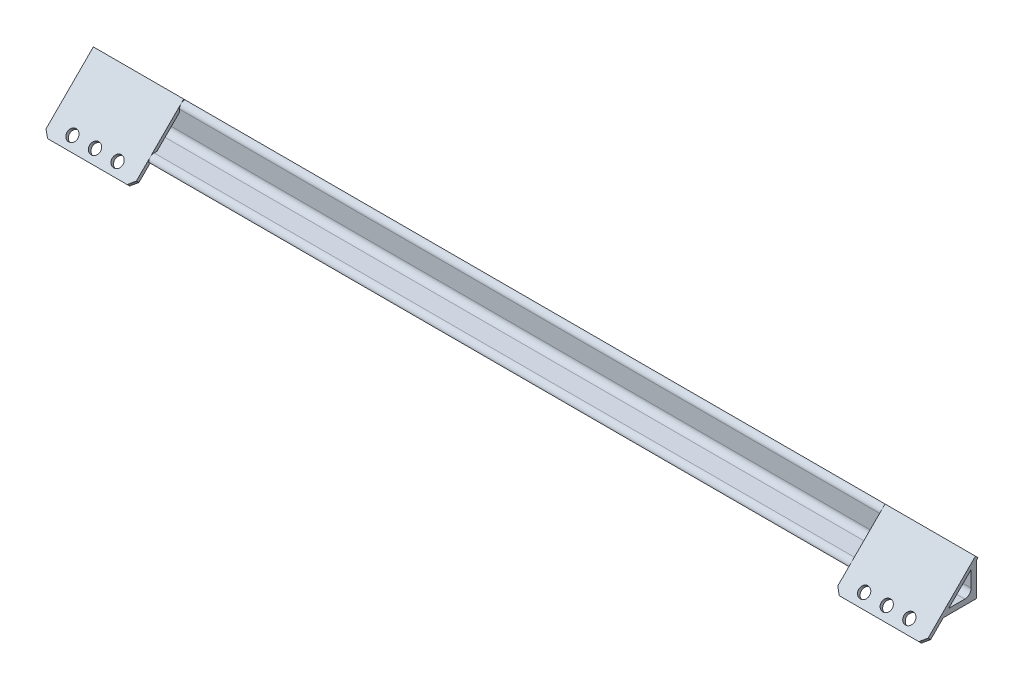
SolidWorks part; units mm, degrees
ref_plane "Alzado" through (0, 0, 0) normal (0, 0, 1) x (1, 0, 0)
ref_plane "Planta" through (0, 0, 0) normal (0, 1, 0) x (1, 0, 0)
ref_plane "Vista lateral" through (0, 0, 0) normal (1, 0, 0) x (0, 0, -1)
sketch "Croquis1" plane through (0, 0, 0) normal (0, 0, 1) x (1, 0, 0)
  line L0 (-244, 0) -> (244, 0)
  point P4 (0, 0)
  dimension "D1" = 488
other "Hierro angular 20 X 20 X 3(1)"
ref_plane "Plano1" through (-244, 0, 0) normal (1, 0, 0) x (0, 1, 0)
sketch "Sketch1" plane through (-244, 0, 0) normal (1, 0, 0) x (0, 1, 0)
  line L0 (0, 0) -> (0, 20)
  line L1 (0, 10) -> (3, 10) construction
  line L2 (3, 17) -> (3, 6.5)
  line L3 (6.5, 3) -> (17, 3)
  line L4 (10, 3) -> (10, 0) construction
  line L5 (20, 0) -> (0, 0)
  arc A0 (20, 0) -> (17, 3) centre (17, 0) ccw
  arc A1 (0, 20) -> (3, 17) centre (0, 17) cw
  arc A2 (6.5, 3) -> (3, 6.5) centre (6.5, 6.5) cw
  point P10 (10, 0)
  point P14 (0, 10)
  point P15 (3, 10)
  point P16 (10, 3)
  point P17 (3, 20)
  point P18 (20, 3)
  point P21 (0, 0)
  dimension "D2" = 3
  dimension "D3" = 20
  dimension "Radius_1" = 3.5
  dimension "D1" = 3
ref_plane "Plano2" through (0, 10.6213, 10.6213) normal (0, 0.7071, 0.7071) x (1, 0, 0)
sketch "Croquis3" plane through (0, 10.6213, 10.6213) normal (0, 0.7071, 0.7071) x (1, 0, 0)
  line L0 (244, -9.8995) -> (-244, -9.8995) construction
  line L1 (244, -9.8995) -> (-244, -9.8995) construction
  line L2 (-244, -9.8995) -> (-244, -28.6795) construction
  line L4 (244, 14.1421) -> (-244, 14.1421) construction
  line L5 (244, 14.1421) -> (-244, 14.1421) construction
  line L6 (-194, -19.8995) -> (-244, -19.8995) construction
  line L7 (-244, 14.1421) -> (-194, 14.1421)
  line L8 (-244, 14.1421) -> (-244, -25.8995)
  line L9 (-244, -25.8995) -> (-194, -25.8995)
  line L10 (-194, 14.1421) -> (-194, -25.8995)
  circle A0 centre (-206.5, -19.8995) radius 3
  circle A1 centre (-219, -19.8995) radius 3
  circle A2 centre (-231.5, -19.8995) radius 3
  dimension "D4" = 6
  dimension "D1" = 50
  dimension "D2" = 16
  dimension "D3" = 6
  dimension "D5" = 12.5
  dimension "D6" = 3
extrude "Saliente-Extruir1" add sketch "Croquis3" against normal blind 2 separate body
chamfer "Chaflán1" distance 3 angle 45 2 edges at (-244, -8.3995, 28.2279) (-194, -8.3995, 28.2279)
mirror "Simetría3" about plane through (0, 0, 0) normal (1, 0, 0) of "Chaflán1", "Saliente-Extruir1"
